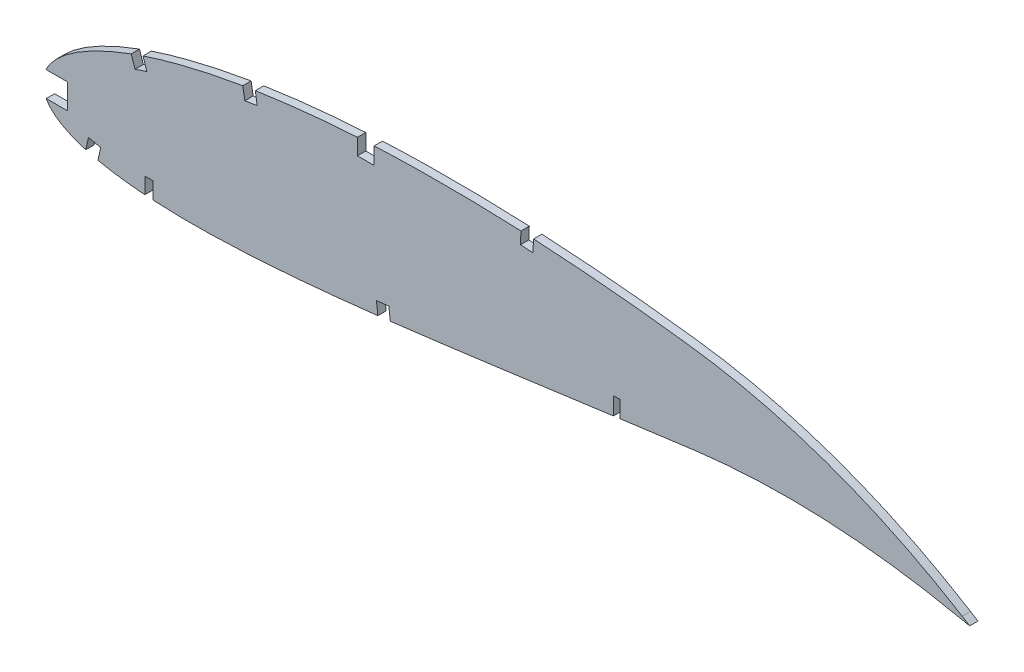
SolidWorks part; units mm, degrees
ref_plane "Front Plane" through (0, 0, 0) normal (0, 0, 1) x (1, 0, 0)
ref_plane "Top Plane" through (0, 0, 0) normal (0, 1, 0) x (1, 0, 0)
ref_plane "Right Plane" through (0, 0, 0) normal (1, 0, 0) x (0, 0, -1)
curve "Curve4"
  spline degree 3 poles (349.8746, 0.5455, 0) (349.8478, 0.562, 0) (349.7407, 0.6282, 0) (349.4993, 0.7762, 0) (349.0975, 1.0228, 0) (348.5349, 1.3661, 0) (347.8121, 1.8054, 0) (346.9286, 2.3375, 0) (345.885, 2.9606, 0) (344.6816, 3.6719, 0) (343.3185, 4.4681, 0) (341.7962, 5.3458, 0) (340.1148, 6.3001, 0) (338.275, 7.3272, 0) (336.2775, 8.422, 0) (334.1225, 9.5798, 0) (331.8109, 10.7946, 0) (329.3436, 12.0612, 0) (326.721, 13.3725, 0) (323.9443, 14.7232, 0) (321.0145, 16.1064, 0) (317.9326, 17.5149, 0) (314.7004, 18.9428, 0) (311.3186, 20.3813, 0) (307.7893, 21.8242, 0) (304.114, 23.2633, 0) (300.2949, 24.6919, 0) (296.3333, 26.1008, 0) (292.2323, 27.484, 0) (287.9939, 28.8323, 0) (283.6211, 30.1385, 0) (279.1164, 31.3942, 0) (274.4837, 32.5927, 0) (269.7257, 33.7256, 0) (264.8466, 34.785, 0) (259.8503, 35.7648, 0) (254.7409, 36.655, 0) (249.5326, 37.455, 0) (244.3091, 38.1205, 0) (239.0964, 38.7732, 0) (233.8915, 39.3864, 0) (228.623, 39.9736, 0) (223.2959, 40.5315, 0) (217.9156, 41.0583, 0) (212.4874, 41.5519, 0) (207.0171, 42.0107, 0) (201.5099, 42.4322, 0) (195.9716, 42.8157, 0) (190.4077, 43.1578, 0) (184.8241, 43.4583, 0) (179.2266, 43.7151, 0) (173.6208, 43.9264, 0) (168.0128, 44.0909, 0) (162.4085, 44.2071, 0) (156.8137, 44.2742, 0) (151.2345, 44.2904, 0) (145.6768, 44.2555, 0) (140.1465, 44.1681, 0) (134.6496, 44.0271, 0) (129.192, 43.8323, 0) (123.7796, 43.5837, 0) (118.4182, 43.2792, 0) (113.1138, 42.9209, 0) (107.8721, 42.5071, 0) (102.6991, 42.0378, 0) (97.6, 41.5149, 0) (92.5806, 40.937, 0) (87.6463, 40.3058, 0) (82.8024, 39.6225, 0) (78.0545, 38.8867, 0) (73.4074, 38.1005, 0) (68.8664, 37.2648, 0) (64.4362, 36.3819, 0) (60.1215, 35.4522, 0) (55.9271, 34.4784, 0) (51.8572, 33.4622, 0) (47.9162, 32.4055, 0) (44.1081, 31.3108, 0) (40.4368, 30.1806, 0) (36.9066, 29.0161, 0) (33.52, 27.8218, 0) (30.2813, 26.5985, 0) (27.193, 25.3499, 0) (24.2586, 24.0778, 0) (21.4804, 22.7861, 0) (18.8615, 21.4761, 0) (16.4038, 20.1517, 0) (14.1097, 18.8148, 0) (11.9815, 17.4679, 0) (10.02, 16.1143, 0) (8.2279, 14.7551, 0) (6.606, 13.3936, 0) (5.1551, 12.0318, 0) (3.8773, 10.6708, 0) (2.7727, 9.3129, 0) (1.8427, 7.9591, 0) (1.0874, 6.6108, 0) (0.5085, 5.269, 0) (0.1055, 3.9344, 0) (-0.1151, 2.6089, 0) (-0.17, 1.2916, 0) (-0.0566, 0.4299, 0) (0, 0, 0) knots 0 0 0 0 0.000254 0.001015 0.002283 0.004057 0.006331 0.009105 0.012374 0.016134 0.02038 0.025106 0.030306 0.035972 0.0421 0.048678 0.055702 0.06316 0.071046 0.07935 0.088063 0.097176 0.106678 0.116562 0.126814 0.137428 0.148394 0.1597 0.171338 0.183298 0.19557 0.208144 0.221012 0.234162 0.247587 0.261277 0.275223 0.289414 0.303771 0.317689 0.331784 0.34604 0.360444 0.374983 0.38964 0.404403 0.419257 0.434187 0.449177 0.464215 0.479284 0.49437 0.509458 0.524532 0.539579 0.554583 0.56953 0.584403 0.599191 0.613877 0.628447 0.642889 0.657186 0.671326 0.685294 0.699078 0.712665 0.726043 0.739198 0.752118 0.764792 0.777208 0.789356 0.801224 0.812804 0.824083 0.835055 0.84571 0.856038 0.866034 0.875689 0.884998 0.893953 0.902553 0.910789 0.918661 0.926166 0.933303 0.940071 0.946475 0.952518 0.958205 0.963547 0.968557 0.97325 0.977651 0.981787 0.985694 0.989415 0.993001 0.996508 1 1 1 1
curve "Curve5"
  spline degree 3 poles (0, 0, 0) (0.0898, -0.4241, 0) (0.27, -1.2744, 0) (0.7593, -2.4983, 0) (1.4064, -3.6749, 0) (2.2249, -4.801, 0) (3.2093, -5.8763, 0) (4.3574, -6.9018, 0) (5.6682, -7.8772, 0) (7.1398, -8.8018, 0) (8.7703, -9.6767, 0) (10.5577, -10.5014, 0) (12.5004, -11.2756, 0) (14.5962, -11.9982, 0) (16.8428, -12.6703, 0) (19.2378, -13.2904, 0) (21.7785, -13.8593, 0) (24.4626, -14.3755, 0) (27.2871, -14.8396, 0) (30.2491, -15.2513, 0) (33.3455, -15.6108, 0) (36.5732, -15.9174, 0) (39.9292, -16.1718, 0) (43.41, -16.3741, 0) (47.0123, -16.5249, 0) (50.7326, -16.6238, 0) (54.5673, -16.6722, 0) (58.5129, -16.6709, 0) (62.5656, -16.6195, 0) (66.7219, -16.5208, 0) (70.9777, -16.3742, 0) (75.3293, -16.1816, 0) (79.7728, -15.9448, 0) (84.3041, -15.6646, 0) (88.9192, -15.3423, 0) (93.6142, -14.9805, 0) (98.3848, -14.58, 0) (103.2269, -14.1432, 0) (108.136, -13.6724, 0) (113.1081, -13.1689, 0) (118.1387, -12.6351, 0) (123.2233, -12.0729, 0) (128.3576, -11.4851, 0) (133.537, -10.8728, 0) (138.7569, -10.2396, 0) (144.0126, -9.5866, 0) (149.2997, -8.9164, 0) (154.6133, -8.2321, 0) (159.9485, -7.5337, 0) (165.3008, -6.826, 0) (170.6651, -6.1086, 0) (176.0366, -5.3852, 0) (181.4105, -4.6578, 0) (186.7814, -3.9269, 0) (192.1447, -3.1954, 0) (197.4954, -2.4653, 0) (202.8282, -1.7368, 0) (208.1384, -1.0133, 0) (213.4205, -0.2949, 0) (218.6696, 0.417, 0) (223.8809, 1.1204, 0) (229.0493, 1.8142, 0) (234.1695, 2.4981, 0) (239.2364, 3.1723, 0) (244.169, 3.8163, 0) (248.9545, 4.4645, 0) (253.6088, 4.9959, 0) (258.2053, 5.4495, 0) (262.7485, 5.8213, 0) (267.2331, 6.1168, 0) (271.654, 6.3381, 0) (276.0058, 6.4882, 0) (280.283, 6.5716, 0) (284.4804, 6.5904, 0) (288.5922, 6.5507, 0) (292.613, 6.4555, 0) (296.5372, 6.3093, 0) (300.3594, 6.1169, 0) (304.0742, 5.8836, 0) (307.6759, 5.6128, 0) (311.1595, 5.3108, 0) (314.5196, 4.9821, 0) (317.7512, 4.6304, 0) (320.8494, 4.263, 0) (323.8094, 3.8825, 0) (326.6267, 3.4951, 0) (329.2966, 3.1046, 0) (331.8151, 2.7161, 0) (334.1781, 2.3332, 0) (336.3819, 1.9612, 0) (338.423, 1.6033, 0) (340.2977, 1.2632, 0) (342.0037, 0.9451, 0) (343.5374, 0.6506, 0) (344.8968, 0.3845, 0) (346.0794, 0.1481, 0) (347.0834, -0.0554, 0) (347.9072, -0.2251, 0) (348.5494, -0.3583, 0) (349.0088, -0.4551, 0) (349.2849, -0.5128, 0) (349.4076, -0.5389, 0) (349.4382, -0.5455, 0) knots 0 0 0 0 0.003638 0.007293 0.011028 0.014901 0.018963 0.023258 0.027821 0.032679 0.037853 0.043362 0.049215 0.055422 0.061989 0.068918 0.076211 0.083868 0.091887 0.100266 0.109 0.118085 0.127515 0.137285 0.147388 0.157816 0.168563 0.179619 0.190977 0.202627 0.21456 0.226767 0.239236 0.251959 0.264924 0.27812 0.291536 0.30516 0.318981 0.332985 0.347163 0.361499 0.375981 0.390597 0.405333 0.420175 0.43511 0.450124 0.465203 0.480333 0.495501 0.51069 0.525887 0.541078 0.556247 0.571382 0.586466 0.601485 0.616424 0.631269 0.646007 0.660621 0.675098 0.689423 0.703582 0.716908 0.730009 0.742952 0.755726 0.76832 0.780724 0.792927 0.804916 0.816679 0.828204 0.839475 0.850481 0.861208 0.871639 0.881763 0.891564 0.901027 0.910139 0.918884 0.927249 0.935221 0.942785 0.949928 0.956638 0.962904 0.968712 0.974054 0.978918 0.983297 0.98718 0.990561 0.993433 0.995791 0.99763 0.998946 0.999737 1 1 1 1
sketch "Sketch1" plane through (0, 0, 0) normal (0, 0, 1) x (1, 0, 0)
  line L24 (349.8746, 0.5455) -> (352.7074, -1.2046)
  line L25 (349.4382, -0.5455) -> (352.7074, -1.2046)
  spline S1 degree 3 poles (-4826.1735, -1302.2326) (84.7421, 69.7383) (-8.0065, 19.4278) (0.7593, -2.4983) (1.4064, -3.6749) (2.2249, -4.801) (3.2093, -5.8763) (4.3574, -6.9018) (5.6682, -7.8772) (7.1398, -8.8018) (8.7703, -9.6767) (10.5577, -10.5014) (12.5004, -11.2756) (14.5962, -11.9982) (16.8428, -12.6703) (19.2378, -13.2904) (21.7785, -13.8593) (24.4626, -14.3755) (27.2871, -14.8396) (30.2491, -15.2513) (33.3455, -15.6108) (36.5732, -15.9174) (39.9292, -16.1718) (43.41, -16.3741) (47.0123, -16.5249) (50.7326, -16.6238) (54.5673, -16.6722) (58.5129, -16.6709) (62.5656, -16.6195) (66.7219, -16.5208) (70.9777, -16.3742) (75.3293, -16.1816) (79.7728, -15.9448) (84.3041, -15.6646) (88.9192, -15.3423) (93.6142, -14.9805) (98.3848, -14.58) (103.2269, -14.1432) (108.136, -13.6724) (113.1081, -13.1689) (118.1387, -12.6351) (123.2233, -12.0729) (128.3576, -11.4851) (133.537, -10.8728) (138.7569, -10.2396) (144.0126, -9.5866) (149.2997, -8.9164) (154.6133, -8.2321) (159.9485, -7.5337) (165.3008, -6.826) (170.6651, -6.1086) (176.0366, -5.3852) (181.4105, -4.6578) (186.7814, -3.9269) (192.1447, -3.1954) (197.4954, -2.4653) (202.8282, -1.7368) (208.1384, -1.0133) (213.4205, -0.2949) (218.6696, 0.417) (223.8809, 1.1204) (229.0493, 1.8142) (234.1695, 2.4981) (239.2364, 3.1723) (244.169, 3.8163) (248.9545, 4.4645) (253.6088, 4.9959) (258.2053, 5.4495) (262.7485, 5.8213) (267.2331, 6.1168) (271.654, 6.3381) (276.0058, 6.4882) (280.283, 6.5716) (284.4804, 6.5904) (288.5922, 6.5507) (292.613, 6.4555) (296.5372, 6.3093) (300.3594, 6.1169) (304.0742, 5.8836) (307.6759, 5.6128) (311.1595, 5.3108) (314.5196, 4.9821) (317.7512, 4.6304) (320.8494, 4.263) (323.8094, 3.8825) (326.6267, 3.4951) (329.2966, 3.1046) (331.8151, 2.7161) (334.1781, 2.3332) (336.3819, 1.9612) (338.423, 1.6033) (340.2977, 1.2632) (342.0037, 0.9451) (343.5374, 0.6506) (344.8968, 0.3845) (346.0794, 0.1481) (347.0834, -0.0554) (347.9072, -0.2251) (348.5494, -0.3583) (349.0088, -0.4551) (365.4113, -3.8787) (379.663, -16.7158) (1432.0031, 4879.4073) knots -0.18653 -0.18653 -0.18653 -0.18653 0.003638 0.007293 0.011028 0.014901 0.018963 0.023258 0.027821 0.032679 0.037853 0.043362 0.049215 0.055422 0.061989 0.068918 0.076211 0.083868 0.091887 0.100266 0.109 0.118085 0.127515 0.137285 0.147388 0.157816 0.168563 0.179619 0.190977 0.202627 0.21456 0.226767 0.239236 0.251959 0.264924 0.27812 0.291536 0.30516 0.318981 0.332985 0.347163 0.361499 0.375981 0.390597 0.405333 0.420175 0.43511 0.450124 0.465203 0.480333 0.495501 0.51069 0.525887 0.541078 0.556247 0.571382 0.586466 0.601485 0.616424 0.631269 0.646007 0.660621 0.675098 0.689423 0.703582 0.716908 0.730009 0.742952 0.755726 0.76832 0.780724 0.792927 0.804916 0.816679 0.828204 0.839475 0.850481 0.861208 0.871639 0.881763 0.891564 0.901027 0.910139 0.918884 0.927249 0.935221 0.942785 0.949928 0.956638 0.962904 0.968712 0.974054 0.978918 0.983297 0.98718 0.990561 0.993433 0.995791 0.99763 0.998946 0.999737 1.138459 1.138459 1.138459 1.138459 only from (0, 0) to (349.4382, -0.5455) construction
  spline S3 degree 3 poles (3018.3823, 4226.7606) (376.7158, -26.0809) (365.4465, -9.0056) (349.4993, 0.7762) (349.0975, 1.0228) (348.5349, 1.3661) (347.8121, 1.8054) (346.9286, 2.3375) (345.885, 2.9606) (344.6816, 3.6719) (343.3185, 4.4681) (341.7962, 5.3458) (340.1148, 6.3001) (338.275, 7.3272) (336.2775, 8.422) (334.1225, 9.5798) (331.8109, 10.7946) (329.3436, 12.0612) (326.721, 13.3725) (323.9443, 14.7232) (321.0145, 16.1064) (317.9326, 17.5149) (314.7004, 18.9428) (311.3186, 20.3813) (307.7893, 21.8242) (304.114, 23.2633) (300.2949, 24.6919) (296.3333, 26.1008) (292.2323, 27.484) (287.9939, 28.8323) (283.6211, 30.1385) (279.1164, 31.3942) (274.4837, 32.5927) (269.7257, 33.7256) (264.8466, 34.785) (259.8503, 35.7648) (254.7409, 36.655) (249.5326, 37.455) (244.3091, 38.1205) (239.0964, 38.7732) (233.8915, 39.3864) (228.623, 39.9736) (223.2959, 40.5315) (217.9156, 41.0583) (212.4874, 41.5519) (207.0171, 42.0107) (201.5099, 42.4322) (195.9716, 42.8157) (190.4077, 43.1578) (184.8241, 43.4583) (179.2266, 43.7151) (173.6208, 43.9264) (168.0128, 44.0909) (162.4085, 44.2071) (156.8137, 44.2742) (151.2345, 44.2904) (145.6768, 44.2555) (140.1465, 44.1681) (134.6496, 44.0271) (129.192, 43.8323) (123.7796, 43.5837) (118.4182, 43.2792) (113.1138, 42.9209) (107.8721, 42.5071) (102.6991, 42.0378) (97.6, 41.5149) (92.5806, 40.937) (87.6463, 40.3058) (82.8024, 39.6225) (78.0545, 38.8867) (73.4074, 38.1005) (68.8664, 37.2648) (64.4362, 36.3819) (60.1215, 35.4522) (55.9271, 34.4784) (51.8572, 33.4622) (47.9162, 32.4055) (44.1081, 31.3108) (40.4368, 30.1806) (36.9066, 29.0161) (33.52, 27.8218) (30.2813, 26.5985) (27.193, 25.3499) (24.2586, 24.0778) (21.4804, 22.7861) (18.8615, 21.4761) (16.4038, 20.1517) (14.1097, 18.8148) (11.9815, 17.4679) (10.02, 16.1143) (8.2279, 14.7551) (6.606, 13.3936) (5.1551, 12.0318) (3.8773, 10.6708) (2.7727, 9.3129) (1.8427, 7.9591) (1.0874, 6.6108) (0.5085, 5.269) (0.1055, 3.9344) (-0.1151, 2.6089) (-1.0968, -20.9427) (103.3134, -37.4738) (-4984.07, -377.4853) knots -0.148602 -0.148602 -0.148602 -0.148602 0.000254 0.001015 0.002283 0.004057 0.006331 0.009105 0.012374 0.016134 0.02038 0.025106 0.030306 0.035972 0.0421 0.048678 0.055702 0.06316 0.071046 0.07935 0.088063 0.097176 0.106678 0.116562 0.126814 0.137428 0.148394 0.1597 0.171338 0.183298 0.19557 0.208144 0.221012 0.234162 0.247587 0.261277 0.275223 0.289414 0.303771 0.317689 0.331784 0.34604 0.360444 0.374983 0.38964 0.404403 0.419257 0.434187 0.449177 0.464215 0.479284 0.49437 0.509458 0.524532 0.539579 0.554583 0.56953 0.584403 0.599191 0.613877 0.628447 0.642889 0.657186 0.671326 0.685294 0.699078 0.712665 0.726043 0.739198 0.752118 0.764792 0.777208 0.789356 0.801224 0.812804 0.824083 0.835055 0.84571 0.856038 0.866034 0.875689 0.884998 0.893953 0.902553 0.910789 0.918661 0.926166 0.933303 0.940071 0.946475 0.952518 0.958205 0.963547 0.968557 0.97325 0.977651 0.981787 0.985694 0.989415 0.993001 0.996508 1.178653 1.178653 1.178653 1.178653 only from (349.8746, 0.5455) to (0, 0) construction
  spline S4 degree 3 poles (0, 0) (0.0898, -0.4241) (0.27, -1.2744) (0.7593, -2.4983) (1.4064, -3.6749) (2.2249, -4.801) (3.2093, -5.8763) (4.3574, -6.9018) (5.6682, -7.8772) (7.1398, -8.8018) (8.7703, -9.6767) (10.5577, -10.5014) (12.5004, -11.2756) (14.5962, -11.9982) (16.8428, -12.6703) (19.2378, -13.2904) (21.7785, -13.8593) (24.4626, -14.3755) (27.2871, -14.8396) (30.2491, -15.2513) (33.3455, -15.6108) (36.5732, -15.9174) (39.9292, -16.1718) (43.41, -16.3741) (47.0123, -16.5249) (50.7326, -16.6238) (54.5673, -16.6722) (58.5129, -16.6709) (62.5656, -16.6195) (66.7219, -16.5208) (70.9777, -16.3742) (75.3293, -16.1816) (79.7728, -15.9448) (84.3041, -15.6646) (88.9192, -15.3423) (93.6142, -14.9805) (98.3848, -14.58) (103.2269, -14.1432) (108.136, -13.6724) (113.1081, -13.1689) (118.1387, -12.6351) (123.2233, -12.0729) (128.3576, -11.4851) (133.537, -10.8728) (138.7569, -10.2396) (144.0126, -9.5866) (149.2997, -8.9164) (154.6133, -8.2321) (159.9485, -7.5337) (165.3008, -6.826) (170.6651, -6.1086) (176.0366, -5.3852) (181.4105, -4.6578) (186.7814, -3.9269) (192.1447, -3.1954) (197.4954, -2.4653) (202.8282, -1.7368) (208.1384, -1.0133) (213.4205, -0.2949) (218.6696, 0.417) (223.8809, 1.1204) (229.0493, 1.8142) (234.1695, 2.4981) (239.2364, 3.1723) (244.169, 3.8163) (248.9545, 4.4645) (253.6088, 4.9959) (258.2053, 5.4495) (262.7485, 5.8213) (267.2331, 6.1168) (271.654, 6.3381) (276.0058, 6.4882) (280.283, 6.5716) (284.4804, 6.5904) (288.5922, 6.5507) (292.613, 6.4555) (296.5372, 6.3093) (300.3594, 6.1169) (304.0742, 5.8836) (307.6759, 5.6128) (311.1595, 5.3108) (314.5196, 4.9821) (317.7512, 4.6304) (320.8494, 4.263) (323.8094, 3.8825) (326.6267, 3.4951) (329.2966, 3.1046) (331.8151, 2.7161) (334.1781, 2.3332) (336.3819, 1.9612) (338.423, 1.6033) (340.2977, 1.2632) (342.0037, 0.9451) (343.5374, 0.6506) (344.8968, 0.3845) (346.0794, 0.1481) (347.0834, -0.0554) (347.9072, -0.2251) (348.5494, -0.3583) (349.0088, -0.4551) (349.2849, -0.5128) (349.4076, -0.5389) (349.4382, -0.5455) knots 0 0 0 0 0.003638 0.007293 0.011028 0.014901 0.018963 0.023258 0.027821 0.032679 0.037853 0.043362 0.049215 0.055422 0.061989 0.068918 0.076211 0.083868 0.091887 0.100266 0.109 0.118085 0.127515 0.137285 0.147388 0.157816 0.168563 0.179619 0.190977 0.202627 0.21456 0.226767 0.239236 0.251959 0.264924 0.27812 0.291536 0.30516 0.318981 0.332985 0.347163 0.361499 0.375981 0.390597 0.405333 0.420175 0.43511 0.450124 0.465203 0.480333 0.495501 0.51069 0.525887 0.541078 0.556247 0.571382 0.586466 0.601485 0.616424 0.631269 0.646007 0.660621 0.675098 0.689423 0.703582 0.716908 0.730009 0.742952 0.755726 0.76832 0.780724 0.792927 0.804916 0.816679 0.828204 0.839475 0.850481 0.861208 0.871639 0.881763 0.891564 0.901027 0.910139 0.918884 0.927249 0.935221 0.942785 0.949928 0.956638 0.962904 0.968712 0.974054 0.978918 0.983297 0.98718 0.990561 0.993433 0.995791 0.99763 0.998946 0.999737 1 1 1 1
  spline S5 degree 3 poles (349.8746, 0.5455) (349.8478, 0.562) (349.7407, 0.6282) (349.4993, 0.7762) (349.0975, 1.0228) (348.5349, 1.3661) (347.8121, 1.8054) (346.9286, 2.3375) (345.885, 2.9606) (344.6816, 3.6719) (343.3185, 4.4681) (341.7962, 5.3458) (340.1148, 6.3001) (338.275, 7.3272) (336.2775, 8.422) (334.1225, 9.5798) (331.8109, 10.7946) (329.3436, 12.0612) (326.721, 13.3725) (323.9443, 14.7232) (321.0145, 16.1064) (317.9326, 17.5149) (314.7004, 18.9428) (311.3186, 20.3813) (307.7893, 21.8242) (304.114, 23.2633) (300.2949, 24.6919) (296.3333, 26.1008) (292.2323, 27.484) (287.9939, 28.8323) (283.6211, 30.1385) (279.1164, 31.3942) (274.4837, 32.5927) (269.7257, 33.7256) (264.8466, 34.785) (259.8503, 35.7648) (254.7409, 36.655) (249.5326, 37.455) (244.3091, 38.1205) (239.0964, 38.7732) (233.8915, 39.3864) (228.623, 39.9736) (223.2959, 40.5315) (217.9156, 41.0583) (212.4874, 41.5519) (207.0171, 42.0107) (201.5099, 42.4322) (195.9716, 42.8157) (190.4077, 43.1578) (184.8241, 43.4583) (179.2266, 43.7151) (173.6208, 43.9264) (168.0128, 44.0909) (162.4085, 44.2071) (156.8137, 44.2742) (151.2345, 44.2904) (145.6768, 44.2555) (140.1465, 44.1681) (134.6496, 44.0271) (129.192, 43.8323) (123.7796, 43.5837) (118.4182, 43.2792) (113.1138, 42.9209) (107.8721, 42.5071) (102.6991, 42.0378) (97.6, 41.5149) (92.5806, 40.937) (87.6463, 40.3058) (82.8024, 39.6225) (78.0545, 38.8867) (73.4074, 38.1005) (68.8664, 37.2648) (64.4362, 36.3819) (60.1215, 35.4522) (55.9271, 34.4784) (51.8572, 33.4622) (47.9162, 32.4055) (44.1081, 31.3108) (40.4368, 30.1806) (36.9066, 29.0161) (33.52, 27.8218) (30.2813, 26.5985) (27.193, 25.3499) (24.2586, 24.0778) (21.4804, 22.7861) (18.8615, 21.4761) (16.4038, 20.1517) (14.1097, 18.8148) (11.9815, 17.4679) (10.02, 16.1143) (8.2279, 14.7551) (6.606, 13.3936) (5.1551, 12.0318) (3.8773, 10.6708) (2.7727, 9.3129) (1.8427, 7.9591) (1.0874, 6.6108) (0.5085, 5.269) (0.1055, 3.9344) (-0.1151, 2.6089) (-0.17, 1.2916) (-0.0566, 0.4299) (0, 0) knots 0 0 0 0 0.000254 0.001015 0.002283 0.004057 0.006331 0.009105 0.012374 0.016134 0.02038 0.025106 0.030306 0.035972 0.0421 0.048678 0.055702 0.06316 0.071046 0.07935 0.088063 0.097176 0.106678 0.116562 0.126814 0.137428 0.148394 0.1597 0.171338 0.183298 0.19557 0.208144 0.221012 0.234162 0.247587 0.261277 0.275223 0.289414 0.303771 0.317689 0.331784 0.34604 0.360444 0.374983 0.38964 0.404403 0.419257 0.434187 0.449177 0.464215 0.479284 0.49437 0.509458 0.524532 0.539579 0.554583 0.56953 0.584403 0.599191 0.613877 0.628447 0.642889 0.657186 0.671326 0.685294 0.699078 0.712665 0.726043 0.739198 0.752118 0.764792 0.777208 0.789356 0.801224 0.812804 0.824083 0.835055 0.84571 0.856038 0.866034 0.875689 0.884998 0.893953 0.902553 0.910789 0.918661 0.926166 0.933303 0.940071 0.946475 0.952518 0.958205 0.963547 0.968557 0.97325 0.977651 0.981787 0.985694 0.989415 0.993001 0.996508 1 1 1 1
extrude "Boss-Extrude1" add sketch "Sketch1" along normal blind 3.175
sketch "Sketch2" plane through (0, 0, 0) normal (0, 0, -1) x (-1, 0, 0)
  line L0 (-219.6066, 6.9148) -> (-217.0666, 6.9148)
  line L1 (-219.6066, 0.5647) -> (-219.6066, 6.9148)
  line L2 (-217.0666, 0.5647) -> (-217.0666, -0.7899)
  line L3 (-125.9441, 43.5934) -> (-125.9441, 37.241)
  line L4 (-217.0666, -0.7899) -> (-219.6066, -0.1126)
  line L5 (-41.8066, -16.2784) -> (-41.8066, -9.9284)
  line L6 (-219.6066, -0.1126) -> (-219.6066, 0.5647)
  line L7 (-38.6316, -16.2784) -> (-38.6316, -9.9284)
  line L8 (-125.9441, 37.241) -> (-119.5941, 37.241)
  line L9 (-119.5941, 43.5934) -> (-119.5941, 37.241)
  line L10 (-125.9441, 43.5934) -> (-125.9441, 46.4957)
  line L11 (-217.0666, 0.5647) -> (-217.0666, 6.9148)
  line L12 (-125.9441, 46.4957) -> (-119.5941, 44.8024)
  line L13 (-119.5941, 44.8024) -> (-119.5941, 43.5934)
  line L14 (-41.8066, -16.2784) -> (-38.6316, -16.2784)
  line L15 (-41.8066, -9.9284) -> (-38.6316, -9.9284)
extrude "Cut-Extrude1" cut sketch "Sketch2" against normal blind 7.62
sketch "Sketch3" plane through (0, 0, 3.175) normal (0, 0, 1) x (1, 0, 0)
  line L1 (-0.4071, 6.4083) -> (9.1179, 6.4083)
  line L2 (16.1715, -12.5452) -> (15.7059, -14.4019)
  line L3 (9.1179, -3.1167) -> (9.1179, 6.4083)
  line L4 (20.793, -13.704) -> (20.3275, -15.5607)
  line L5 (39.4213, 24.9477) -> (37.9149, 29.4655)
  line L6 (15.7059, -14.4019) -> (20.3275, -15.5607)
  line L7 (20.793, -13.704) -> (21.8392, -8.9067)
  line L9 (21.8392, -8.9067) -> (17.1861, -7.8921)
  line L10 (127.3683, -11.6175) -> (127.6344, -13.8855)
  line L11 (81.4236, 34.6803) -> (80.6994, 39.3875)
  line L12 (132.1136, -11.0609) -> (132.3796, -13.3289)
  line L13 (132.1136, -11.0609) -> (131.5505, -6.3243)
  line L14 (127.6344, -13.8855) -> (132.3796, -13.3289)
  line L15 (131.5505, -6.3243) -> (126.8213, -6.8865)
  line L17 (186.4034, 38.6915) -> (186.6522, 43.4474)
  line L19 (-0.4071, -3.1167) -> (-0.4071, 6.4083)
  line L21 (-0.4071, -3.1167) -> (9.1179, -3.1167)
  line L23 (33.4172, 27.8983) -> (34.9034, 23.4412)
  line L25 (34.9034, 23.4412) -> (39.4213, 24.9477)
  line L27 (17.1861, -7.8921) -> (16.1715, -12.5452)
  line L29 (75.932, 38.6201) -> (76.7164, 33.9561)
  line L31 (76.7164, 33.9561) -> (81.4236, 34.6803)
  line L33 (126.8213, -6.8865) -> (127.3683, -11.6175)
  line L35 (181.8631, 43.6817) -> (181.6474, 38.9402)
  line L37 (181.6474, 38.9402) -> (186.4034, 38.6915)
  arc A1 (186.6522, 43.4474) -> (181.8631, 43.6817) centre (149.7221, -662.3427) ccw
  spline S1 degree 3 poles (37.9149, 29.4655) (37.5031, 29.3282) (35.9987, 28.8207) (34.5011, 28.2932) (33.4172, 27.8983) knots 0 0 0 0 0.273428 1 1 1 1
  spline S3 degree 3 poles (80.6994, 39.3875) (79.7758, 39.2454) (78.1859, 38.9943) (76.5977, 38.7321) (75.932, 38.6201) knots 0 0 0 0 0.580571 1 1 1 1
extrude "Cut-Extrude2" cut sketch "Sketch3" against normal blind 7.62
